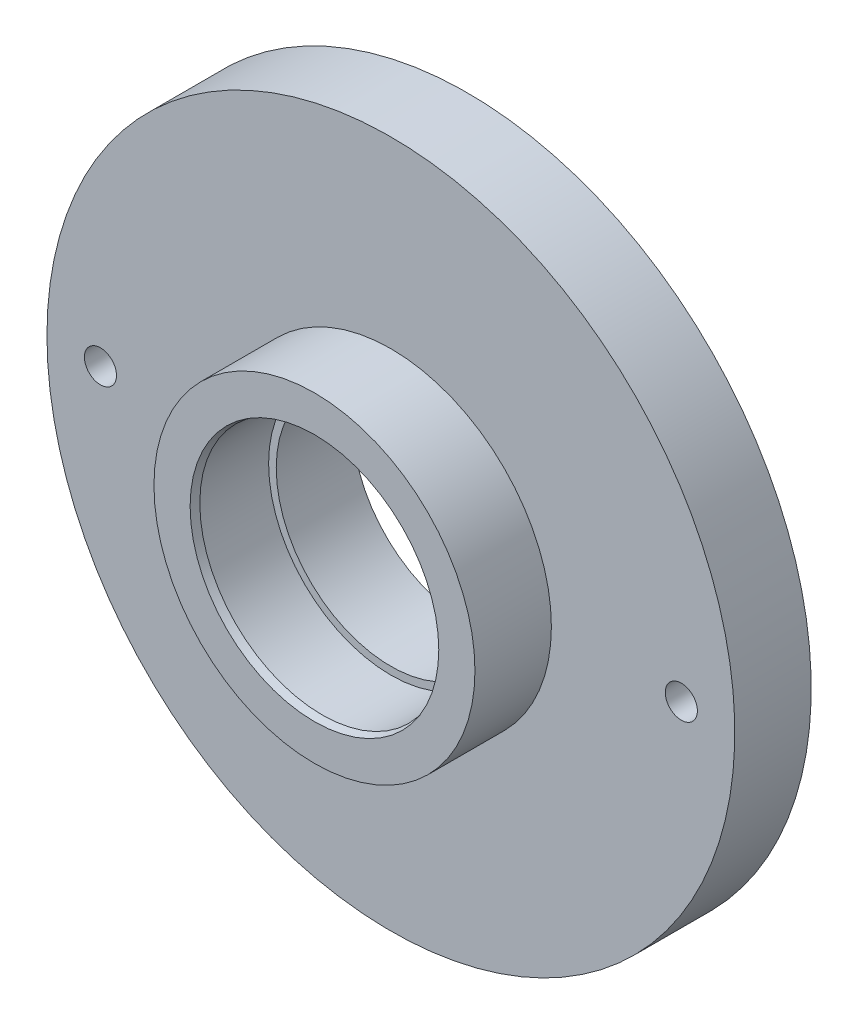
SolidWorks part; units mm, degrees
ref_plane "Front Plane" through (0, 0, 0) normal (0, 0, 1) x (1, 0, 0)
ref_plane "Top Plane" through (0, 0, 0) normal (0, 1, 0) x (1, 0, 0)
ref_plane "Right Plane" through (0, 0, 0) normal (1, 0, 0) x (0, 0, -1)
sketch "Sketch1" plane through (0, 0, 0) normal (0, 1, 0) x (1, 0, 0)
  line L0 (16, 0) -> (16, 10)
  line L1 (16, 10) -> (15, 10)
  line L2 (16, 0) -> (21, 0)
  line L3 (21, 0) -> (21, 10)
  line L4 (21, 10) -> (45, 10)
  line L5 (45, 10) -> (45, 20)
  line L6 (45, 20) -> (15, 20)
  line L7 (15, 20) -> (15, 10)
  line L8 (0, 0) -> (0, -29.3067) construction
  dimension "D1" = 16
  dimension "D2" = 5
  dimension "D3" = 10
  dimension "D4" = 10
  dimension "D5" = 10
  dimension "D6" = 45
  dimension "D7" = 15
revolve "Revolve1" add sketch "Sketch1" angle 360 about L8
chamfer "Chamfer1" distance 1 angle 15 1 edges at (-16, 0, 0)
sketch "Sketch2" plane through (0, 0, -10) normal (0, 0, 1) x (1, 0, 0)
  line L0 (-38, 0) -> (38, 0) construction
  line L1 (-38, 0) -> (-45, 0) construction
  circle A0 centre (-38, 0) radius 2 construction
  circle A1 centre (38, 0) radius 2 construction
  circle A2 centre (0, 0) radius 45 construction
  circle A3 centre (0, 0) radius 45 construction
  point P4 (0, 0)
  dimension "D2" = 4
  dimension "D3" = 4
  dimension "D1" = 7
ref_point "Point1"
ref_point "Point2"
hole_wizard "M5 Tapped Hole1" positions "Sketch13" profile "Sketch15" tap size "M5" standard "DIN" end condition through all
sketch "Sketch13" plane through (0, 0, -10) normal (0, 0, 1) x (1, 0, 0)
  point P0 (-38, 0)
  point P3 (38, 0)
sketch "Sketch15" plane through (-38, 0, -10) normal (1, 0, 0) x (0, -1, 0)
  line L0 (0, 0) -> (0, 10)
  line L1 (0, 10) -> (2.1, 10)
  line L2 (2.1, 10) -> (2.1, 0)
  line L5 (2.1, 0) -> (0, 0)
  line L11 (0, -6.35) -> (0, 107.95) construction
  dimension "Thru Tap Drill Dia." = 4.2
  dimension "Thru Tap Drill Depth" = 10
cosmetic thread "Hole Thread1" parameters "D2"=5
cosmetic thread "Hole Thread2" parameters "D2"=5
